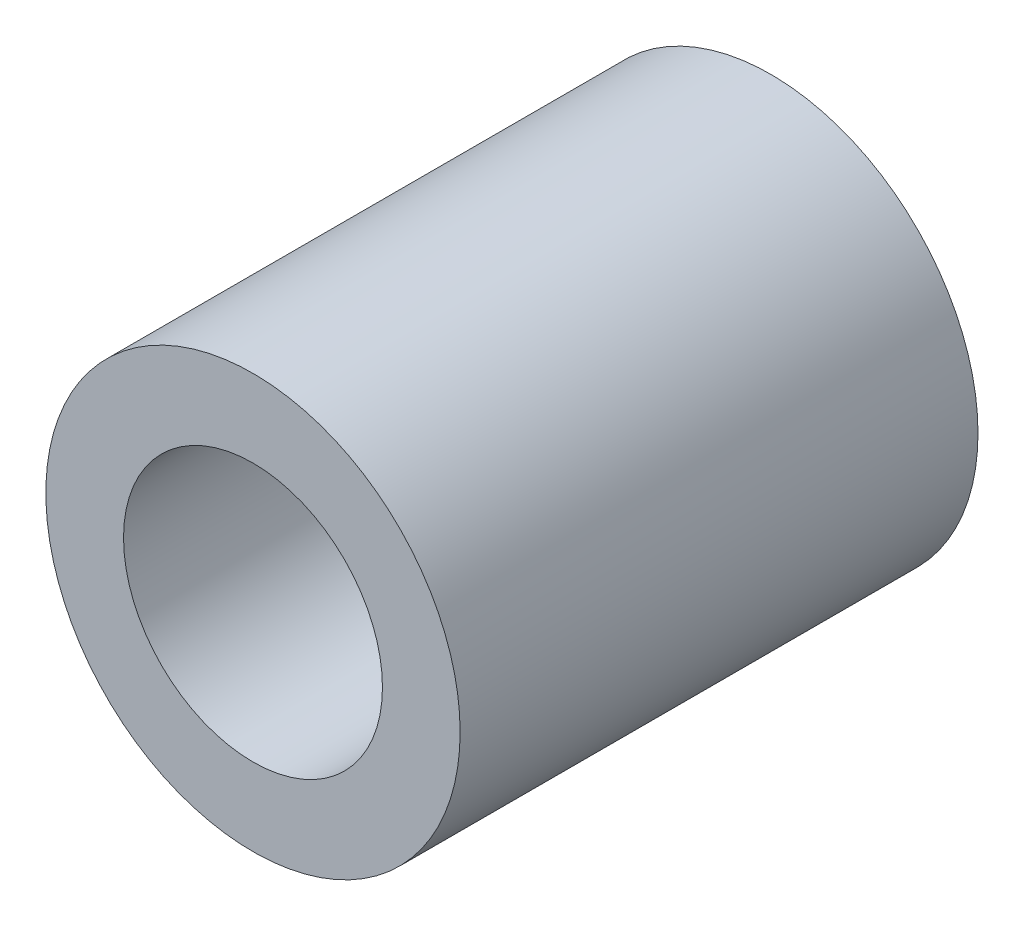
SolidWorks part; units mm, degrees
ref_plane "Alzado" through (0, 0, 0) normal (0, 0, 1) x (1, 0, 0)
ref_plane "Planta" through (0, 0, 0) normal (0, 1, 0) x (1, 0, 0)
ref_plane "Vista lateral" through (0, 0, 0) normal (1, 0, 0) x (0, 0, -1)
sketch "Croquis1" plane through (0, 0, 0) normal (0, 0, 1) x (1, 0, 0)
  circle A0 centre (0, 0) radius 4
  circle A1 centre (0, 0) radius 2.5
  dimension "D1" = 5
  dimension "D2" = 8
extrude "Saliente-Extruir1" add sketch "Croquis1" along normal blind 10
